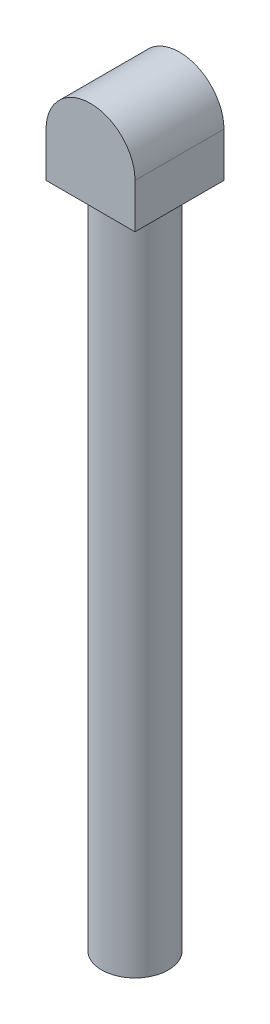
SolidWorks part; units mm, degrees
ref_plane "Front" through (0, 0, 0) normal (0, 0, 1) x (1, 0, 0)
ref_plane "Top" through (0, 0, 0) normal (0, 1, 0) x (1, 0, 0)
ref_plane "Right" through (0, 0, 0) normal (1, 0, 0) x (0, 0, -1)
sketch "草图1" plane through (0, 0, 0) normal (0, 1, 0) x (1, 0, 0)
  line L1 (-4, 4) -> (4, 4)
  line L2 (-4, 4) -> (-4, -4)
  line L3 (-4, -4) -> (4, -4)
  line L4 (4, 4) -> (4, -4)
  dimension "D1" = 8
  dimension "D2" = 8
  dimension "D3" = 4
  dimension "D4" = 4
extrude "凸台-拉伸1" add sketch "草图1" along normal blind 8
sketch "草图2" plane through (0, 0, 4) normal (0, 0, 1) x (1, 0, 0)
  line L6 (-4, 4) -> (-4, 9.4233)
  line L7 (-4, 9.4233) -> (4, 9.4233)
  line L8 (4, 4) -> (4, 9.4233)
  arc A0 (4, 4) -> (-4, 4) centre (0, 4) ccw
extrude "切除-拉伸1" cut sketch "草图2" against normal blind 8
sketch "草图3" plane through (0, 0, 0) normal (0, -1, 0) x (1, 0, 0)
  circle A0 centre (0, 0) radius 3
extrude "凸台-拉伸2" add sketch "草图3" along normal blind 60
